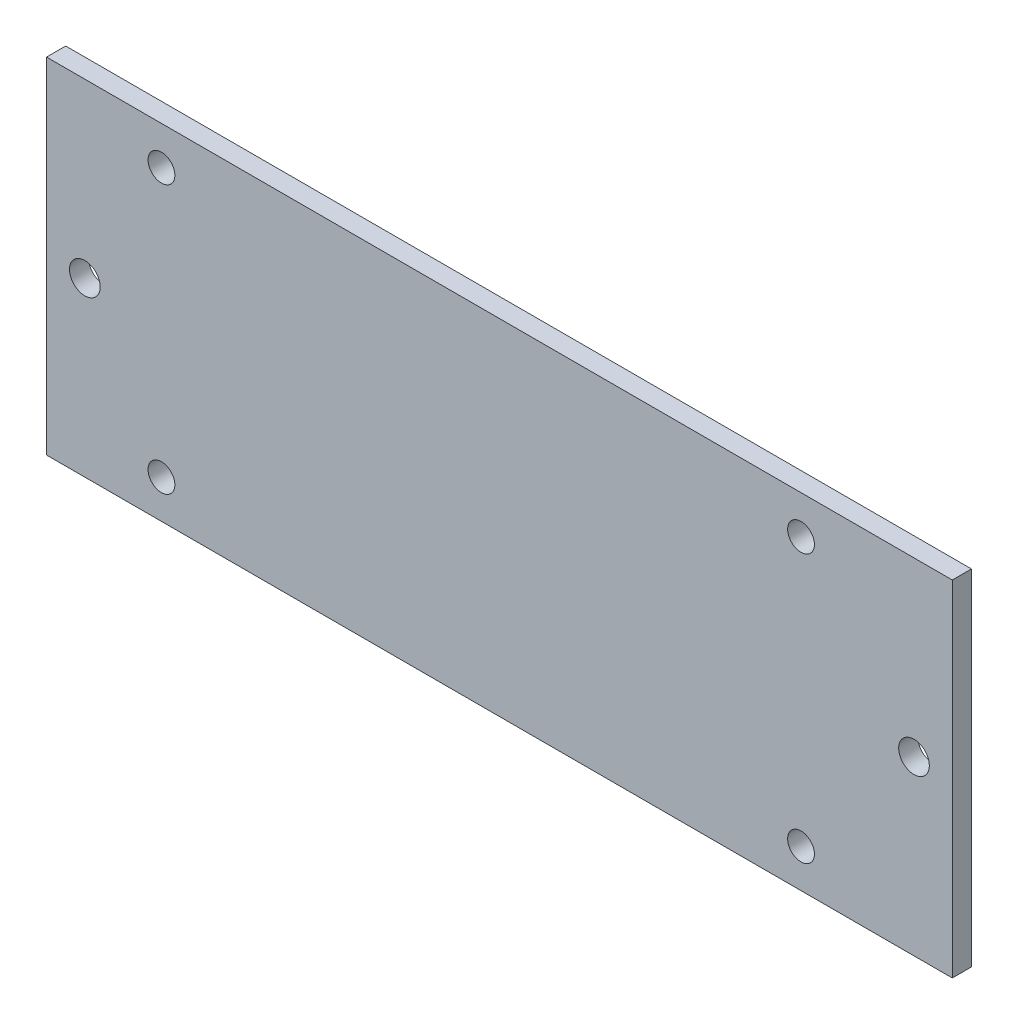
SolidWorks part; units mm, degrees
ref_plane "Front Plane" through (0, 0, 0) normal (0, 0, 1) x (1, 0, 0)
ref_plane "Top Plane" through (0, 0, 0) normal (0, 1, 0) x (1, 0, 0)
ref_plane "Right Plane" through (0, 0, 0) normal (1, 0, 0) x (0, 0, -1)
sketch "Sketch1" plane through (0, 0, 0) normal (0, 0, 1) x (1, 0, 0)
  line L1 (-44.9669, 18.9503) -> (15.1041, 18.9503)
  line L2 (-44.9669, 18.9503) -> (-44.9669, -3.9097)
  line L3 (-44.9669, -3.9097) -> (15.1041, -3.9097)
  line L4 (15.1041, 18.9503) -> (15.1041, -3.9097)
  dimension "D1" = 60.071
  dimension "D2" = 22.86
extrude "Boss-Extrude1" add sketch "Sketch1" along normal blind 1.27
sketch "Sketch2" plane through (0, 0, 1.27) normal (0, 0, 1) x (1, 0, 0)
  line L0 (-44.9669, 18.9503) -> (-44.9669, -3.9097) construction
  line L2 (15.1041, 18.9503) -> (-44.9669, 18.9503) construction
  line L3 (15.1041, -3.9097) -> (15.1041, 18.9503) construction
  line L4 (-44.9669, -3.9097) -> (15.1041, -3.9097) construction
  circle A2 centre (-37.3469, 16.4103) radius 0.889
  circle A3 centre (5.0711, 16.4103) radius 0.889
  circle A4 centre (-37.3469, -1.3697) radius 0.889
  circle A5 centre (5.0711, -1.3697) radius 0.889
  circle A6 centre (-42.4269, 7.5203) radius 1.016
  circle A7 centre (12.5641, 7.5203) radius 1.016
  dimension "D1" = 2.54
  dimension "D5" = 17.78
  dimension "D2" = 2.54
  dimension "D3" = 11.43
  dimension "D6" = 2.54
  dimension "D7" = 42.418
  dimension "D8" = 7.62
extrude "Cut-Extrude1" cut sketch "Sketch2" against normal blind 2.54
